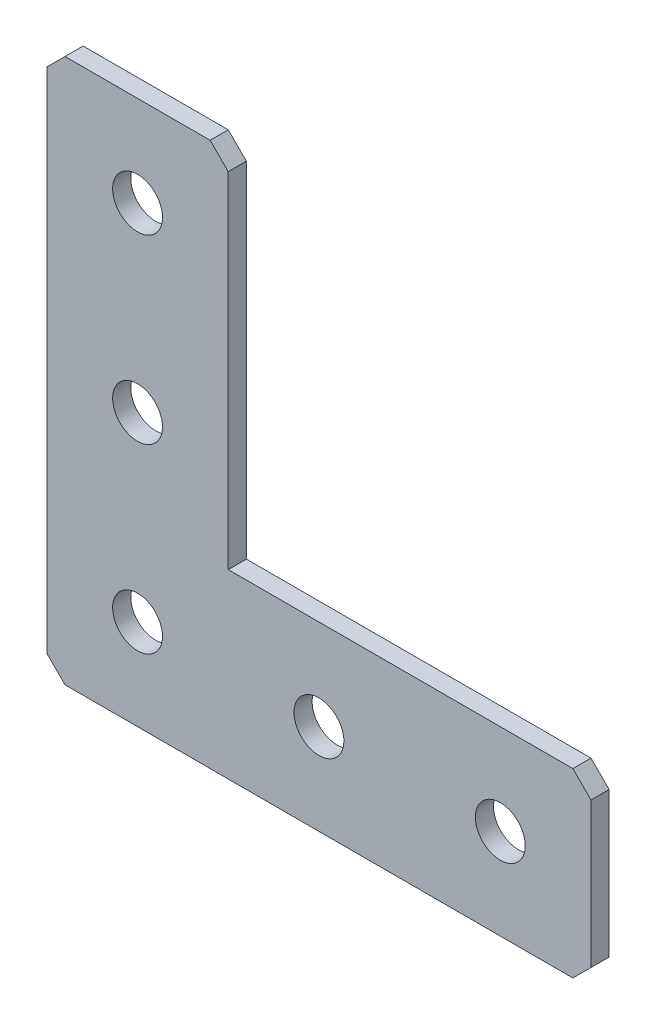
SolidWorks part; units mm, degrees
material "Простая углеродистая сталь"
ref_plane "Спереди(Плоскость XY)" through (0, 0, 0) normal (0, 0, 1) x (1, 0, 0)
ref_plane "Сверху(Плоскость XZ)" through (0, 0, 0) normal (0, 1, 0) x (1, 0, 0)
ref_plane "Справа(Плоскость ZY)" through (0, 0, 0) normal (1, 0, 0) x (0, 0, -1)
sketch "Эскиз1" plane through (0, 0, 0) normal (0, 0, -1) x (1, 0, 0)
  line L0 (0, 0) -> (0, 60)
  line L1 (0, 60) -> (60, 60)
  line L2 (60, 60) -> (60, 40)
  line L3 (60, 40) -> (20, 40)
  line L4 (20, 40) -> (20, 0)
  line L5 (20, 0) -> (0, 0)
  dimension "D1" = 60
  dimension "D3" = 20
extrude "Бобышка-Вытянуть1" add sketch "Эскиз1" along normal blind 2
hole_wizard "Отверстие с зазором M51" positions "Эскиз2" profile "Эскиз3" hole size "M5" standard "DIN" end condition through all
sketch "Эскиз2" plane through (0, 0, -2) normal (0, 0, -1) x (1, 0, 0)
  line L0 (10, 0) -> (10, 60) construction
  line L1 (0, 0) -> (20, 0) construction
  line L2 (60, 60) -> (0, 60) construction
  line L3 (60, 50) -> (0, 50) construction
  line L4 (60, 40) -> (60, 60) construction
  line L5 (0, 60) -> (0, 0) construction
  point P0 (30, 50)
  point P2 (10, 50)
  point P4 (10, 30)
  point P6 (10, 10)
  point P21 (50, 50)
  dimension "D1" = 20
  dimension "D2" = 20
  dimension "D3" = 20
  dimension "D4" = 10
  dimension "D5" = 20
sketch "Эскиз3" plane through (30, -50, -2) normal (1, 0, 0) x (0, 1, 0)
  line L0 (0, 0) -> (0, 2)
  line L1 (0, 2) -> (2.75, 2)
  line L2 (2.75, 2) -> (2.75, 0)
  line L5 (2.75, 0) -> (0, 0)
  line L11 (0, -6.35) -> (0, 107.95) construction
  dimension "Диаметр сквозного отверстия" = 5.5
  dimension "Глубина сквозного отверстия" = 2
chamfer "Фаска1" distance 2 angle 45 5 edges at (0, 0, -1) (20, 0, -1) (60, -40, -1) (60, -60, -1) (0, -60, -1)
